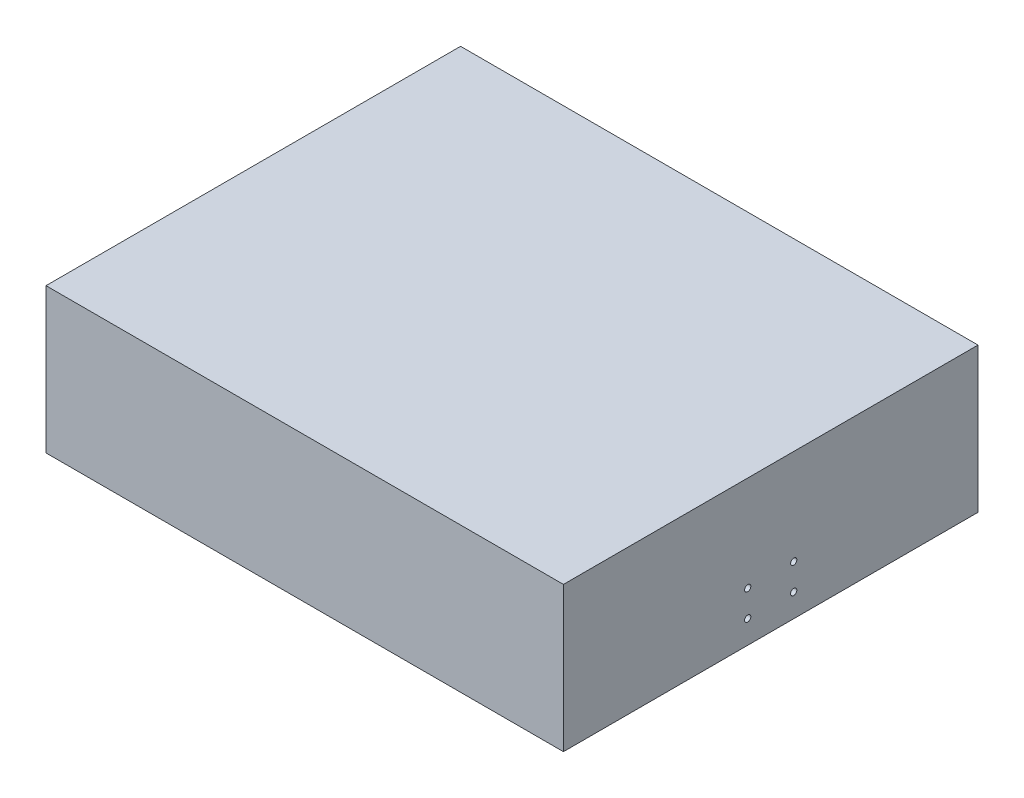
SolidWorks part; units mm, degrees
ref_plane "Front Plane" through (0, 0, 0) normal (0, 0, 1) x (1, 0, 0)
ref_plane "Top Plane" through (0, 0, 0) normal (0, 1, 0) x (1, 0, 0)
ref_plane "Right Plane" through (0, 0, 0) normal (1, 0, 0) x (0, 0, -1)
sketch "Sketch1" plane through (0, 0, 0) normal (0, 1, 0) x (1, 0, 0)
  line L0 (0, 100.15) -> (0, -100.15) construction
  line L1 (125, 0) -> (-128.0777, 0) construction
  line L2 (-125, 100.15) -> (125, 100.15)
  line L3 (125, 100.15) -> (125, -100.15)
  line L4 (125, -100.15) -> (-125, -100.15)
  line L5 (-125, -100.15) -> (-125, 100.15)
  point P7 (0, 100.15)
  point P10 (-125, 0)
  point P11 (0, 0)
  dimension "D1" = 250
  dimension "D2" = 200.3
extrude "Boss-Extrude1" add sketch "Sketch1" along normal blind 70
sketch "Sketch2" plane through (0, 0, 0) normal (0, -1, 0) x (1, 0, 0)
  line L0 (-125, -100.15) -> (-125, 100.15) construction
  line L1 (-115, 90.15) -> (115, 90.15)
  line L2 (-115, 90.15) -> (-115, -90.15)
  line L3 (-115, -90.15) -> (115, -90.15)
  line L4 (115, 90.15) -> (115, -90.15)
  line L5 (125, -100.15) -> (-125, -100.15) construction
  line L6 (-125, 100.15) -> (125, 100.15) construction
  line L7 (125, 100.15) -> (125, -100.15) construction
  dimension "D1" = 10
  dimension "D2" = 10
  dimension "D3" = 10
  dimension "D4" = 10
extrude "Cut-Extrude1" cut sketch "Sketch2" against normal blind 60
sketch "Sketch3" plane through (125, 0, 0) normal (1, 0, 0) x (0, 0, -1)
  line L0 (-100.15, 0) -> (100.15, 0) construction
  line L1 (0, 0) -> (0, 70) construction
  line L2 (-100.15, 70) -> (100.15, 70) construction
  circle A0 centre (-11.115, 23.9) radius 1.5
  circle A1 centre (11.11, 23.9001) radius 1.5
  circle A2 centre (-11.115, 11.2) radius 1.5
  circle A3 centre (11.11, 11.2) radius 1.5
  dimension "D1" = 3
  dimension "D2" = 3
  dimension "D3" = 3
  dimension "D4" = 3
  dimension "D7" = 11.2
  dimension "D8" = 12.7
  dimension "D12" = 11.115
  dimension "D5" = 22.225
  dimension "D6" = 22.225
  dimension "D9" = 12.7001
  dimension "D10" = 11.2
  dimension "D11" = 23.9
extrude "Cut-Extrude2" cut sketch "Sketch3" against normal blind 5
sketch "Sketch4" plane through (0, 0, 0) normal (0, -1, 0) x (1, 0, 0)
  line L0 (125, -100.15) -> (-125, -100.15) construction
  line L1 (-125, 100.15) -> (125, 100.15) construction
  line L2 (-125, -100.15) -> (-125, 100.15) construction
  line L3 (125, 100.15) -> (125, -100.15) construction
  line L4 (-100.15, 95.15) -> (-100.15, -95.15) construction
  line L5 (-100.15, -95.15) -> (110, -95.15) construction
  line L6 (110, -95.15) -> (110, 95.15) construction
  line L7 (110, 95.15) -> (-100.15, 95.15) construction
  circle A0 centre (-100.15, 95.15) radius 2.5
  circle A1 centre (-100.15, -95.15) radius 2.5
  circle A2 centre (110, -95.15) radius 2.5
  circle A3 centre (110, 95.15) radius 2.5
  dimension "D1" = 5
  dimension "D2" = 5
  dimension "D3" = 5
  dimension "D4" = 5
  dimension "D5" = 5
  dimension "D6" = 5
  dimension "D7" = 24.85
  dimension "D8" = 24.85
  dimension "D9" = 15
  dimension "D10" = 5
  dimension "D11" = 15
  dimension "D12" = 5
extrude "Cut-Extrude3" cut sketch "Sketch4" against normal blind 8
